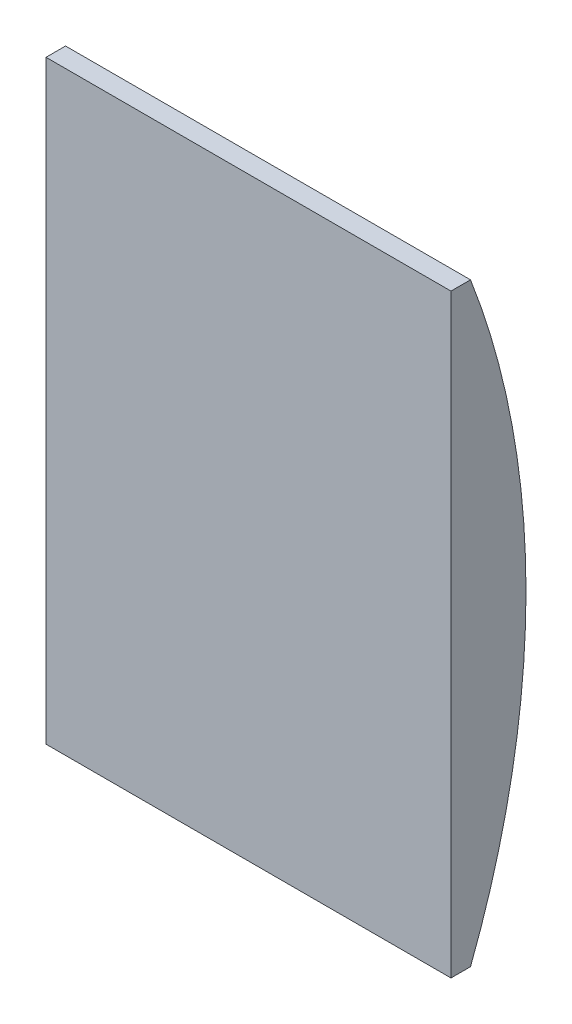
SolidWorks part; units mm, degrees
ref_plane "Front Plane" through (0, 0, 0) normal (0, 0, 1) x (1, 0, 0)
ref_plane "Top Plane" through (0, 0, 0) normal (0, 1, 0) x (1, 0, 0)
ref_plane "Right Plane" through (0, 0, 0) normal (1, 0, 0) x (0, 0, -1)
sketch "Sketch1" plane through (0, 0, 0) normal (1, 0, 0) x (0, 0, -1)
  line L0 (0, 94.869) -> (3.114, 94.869)
  line L1 (0, 0) -> (3.114, 0)
  line L2 (0, 0) -> (0, 94.869)
  line L3 (0, 47.4345) -> (11.9609, 47.4345) construction
  arc A0 (3.114, 94.869) -> (3.114, 0) centre (-119.6287, 47.4345) cw
  dimension "D1" = 3.114
  dimension "D2" = 3.114
  dimension "D3" = 94.869
  dimension "D4" = 11.9609
extrude "Boss-Extrude1" add sketch "Sketch1" along normal blind 64.5795
